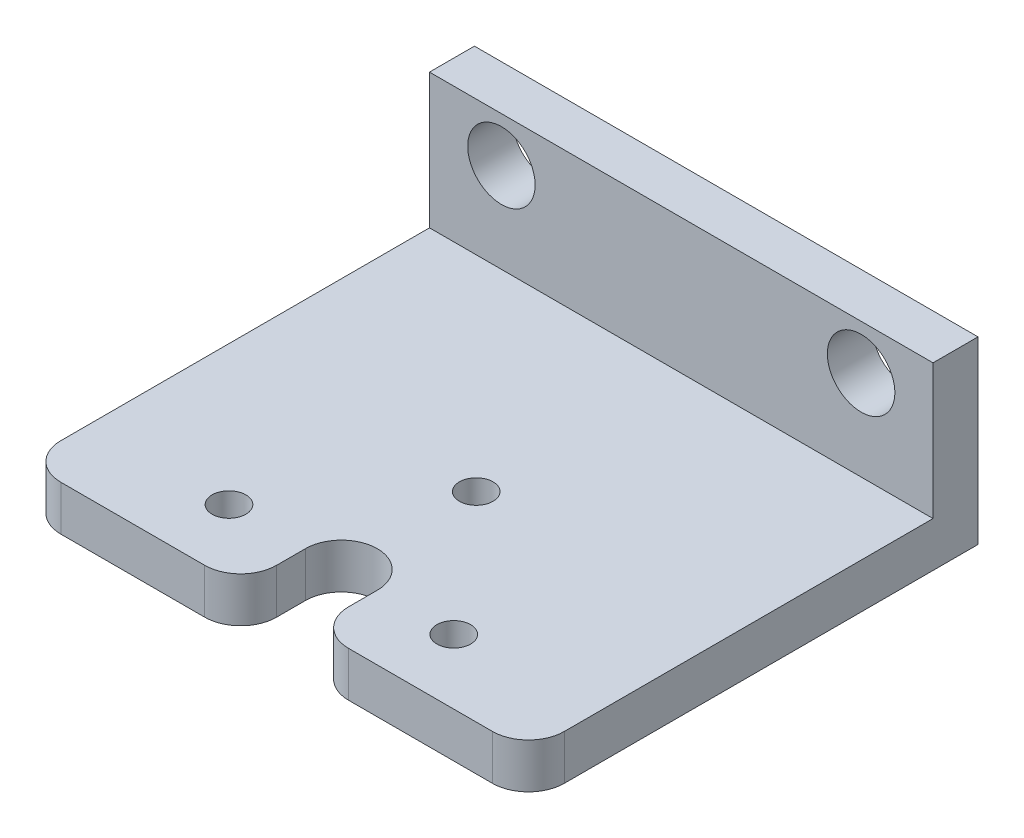
SolidWorks part; units mm, degrees
ref_plane "Front Plane" through (0, 0, 0) normal (0, 0, 1) x (1, 0, 0)
ref_plane "Top Plane" through (0, 0, 0) normal (0, 1, 0) x (1, 0, 0)
ref_plane "Right Plane" through (0, 0, 0) normal (1, 0, 0) x (0, 0, -1)
sketch "Sketch1" plane through (0, 0, 0) normal (0, 0, 1) x (1, 0, 0)
  line L0 (0, 6.35) -> (0, -6.35) construction
  line L1 (-17.78, 6.35) -> (17.78, 6.35)
  line L2 (-17.78, 6.35) -> (-17.78, -6.35)
  line L3 (-17.78, -6.35) -> (17.78, -6.35)
  line L4 (17.78, 6.35) -> (17.78, -6.35)
  circle A0 centre (-12.7, 3.175) radius 2.3813
  circle A1 centre (12.7, 3.175) radius 2.3813
  point P0 (0, 0)
  dimension "D4" = 25.4
  dimension "D1" = 17.78
  dimension "D2" = 12.7
  dimension "D3" = 17.78
extrude "Boss-Extrude1" add sketch "Sketch1" along normal blind 3.175
sketch "Sketch7" plane through (0, 0, 3.175) normal (0, 0, 1) x (1, 0, 0)
  line L1 (-17.78, -3.175) -> (17.78, -3.175)
  line L2 (-17.78, -3.175) -> (-17.78, -6.35)
  line L3 (-17.78, -6.35) -> (17.78, -6.35)
  line L4 (17.78, -3.175) -> (17.78, -6.35)
  line L5 (-17.78, -3.175) -> (17.78, -6.35) construction
  line L6 (-17.78, -6.35) -> (17.78, -3.175) construction
  point P0 (0, -4.7625)
  dimension "D1" = 3.175
extrude "Boss-Extrude3" add sketch "Sketch7" along normal blind 28.575
sketch "Sketch11" plane through (0, -6.35, 0) normal (0, -1, 0) x (1, 0, 0)
  line L0 (17.78, 31.75) -> (17.78, 0) construction
  line L1 (-17.78, 0) -> (17.78, 0) construction
  line L2 (-17.78, 27.178) -> (17.78, 27.178) construction
  line L3 (-2.54, 48.2618) -> (2.54, 48.2618)
  line L4 (-2.54, 48.2618) -> (-2.54, 27.178)
  line L5 (-17.78, 31.75) -> (-17.78, 0) construction
  line L6 (2.54, 48.2618) -> (2.54, 27.178)
  line L7 (0, 31.75) -> (0, 12.219) construction
  line L9 (-17.78, 31.75) -> (17.78, 31.75) construction
  circle A0 centre (-7.9375, 27.178) radius 1.1906
  circle A1 centre (7.9375, 27.178) radius 1.1906
  arc A2 (-2.54, 27.178) -> (2.54, 27.178) centre (0, 27.178) ccw
  circle A3 centre (0, 17.653) radius 1.1906
  point P17 (-12.3447, 26.9875)
  point P26 (12.3447, 26.9875)
  dimension "D3" = 7.9375
  dimension "D2" = 27.178
  dimension "D1" = 17.78
  dimension "D4" = 9.525
extrude "Cut-Extrude1" cut sketch "Sketch11" against normal through all
fillet "Fillet1" radius 2.54 4 edges at (-17.78, -4.7625, 31.75) (17.78, -4.7625, 31.75) (2.54, -4.7625, 31.75) (-2.54, -4.7625, 31.75)
chamfer "Chamfer2" distance 1.27 angle 45 3 edges at (6.7469, -6.35, 27.178) (1.1906, -6.35, 17.653) (-6.7469, -6.35, 27.178)
